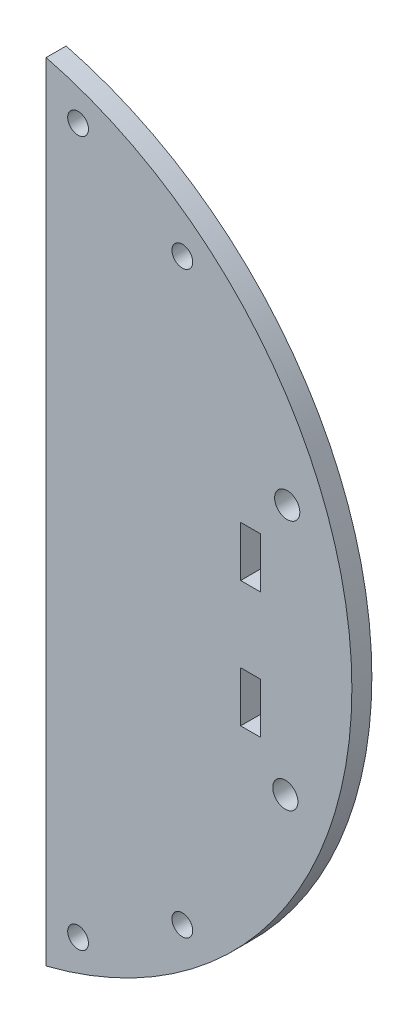
SolidWorks part; units mm, degrees
material "Acrylic (Medium-high impact)"
ref_plane "Front Plane" through (0, 0, 0) normal (0, 0, 1) x (1, 0, 0)
ref_plane "Top Plane" through (0, 0, 0) normal (0, 1, 0) x (1, 0, 0)
ref_plane "Right Plane" through (0, 0, 0) normal (1, 0, 0) x (0, 0, -1)
sketch "Sketch1" plane through (0, 0, 0) normal (0, 0, 1) x (-1, 0, 0)
  line L0 (0, 0) -> (-48.575, 0.3664) construction
  line L3 (0, -62.1367) -> (0, 62.8696)
  circle A15 centre (-5.075, 56.3664) radius 1.65
  circle A16 centre (-21.6385, 46.3664) radius 1.65
  circle A21 centre (-5.075, -55.6336) radius 1.65
  circle A22 centre (-21.6385, -45.6336) radius 1.65
  arc A23 (0, 62.8696) -> (0, -62.1367) centre (15.925, 0.3664) ccw
  circle A24 centre (-38, 20.2872) radius 2
  circle A25 centre (-38.3017, -19.7116) radius 2
  point P2 (15.925, 0.3664)
  dimension "D3" = 4
  dimension "D4" = 20
  dimension "D10" = 3.3
  dimension "D2" = 64.5
  dimension "D5" = 38
extrude "Boss-Extrude1" add sketch "Sketch1" along normal blind 3.175
sketch "Sketch2" plane through (0, 0, 3.175) normal (0, 0, 1) x (1, 0, 0)
  line L0 (0, -0.3664) -> (48.575, -0.3664) construction
  line L1 (0, 62.1367) -> (0, -62.8696) construction
  line L2 (30.9, -6.3664) -> (34.075, -14.3664) construction
  line L3 (30.9, 13.6336) -> (34.075, 13.6336)
  line L4 (30.9, 13.6336) -> (30.9, 5.6336)
  line L5 (30.9, 5.6336) -> (34.075, 5.6336)
  line L6 (34.075, 13.6336) -> (34.075, 5.6336)
  line L7 (30.9, 13.6336) -> (34.075, 5.6336) construction
  line L8 (30.9, 5.6336) -> (34.075, 13.6336) construction
  line L9 (30.9, -14.3664) -> (34.075, -6.3664) construction
  line L10 (34.075, -14.3664) -> (34.075, -6.3664)
  line L11 (30.9, -6.3664) -> (34.075, -6.3664)
  line L12 (30.9, -14.3664) -> (30.9, -6.3664)
  line L13 (30.9, -14.3664) -> (34.075, -14.3664)
  arc A0 (0, -62.8696) -> (0, 62.1367) centre (-15.925, -0.3664) ccw construction
  point P7 (32.4875, 9.6336)
  point P16 (32.4875, -10.3664)
  dimension "D1" = 8
  dimension "D2" = 3.175
  dimension "D3" = 6
  dimension "D4" = 50
extrude "Cut-Extrude1" cut sketch "Sketch2" against normal through all
